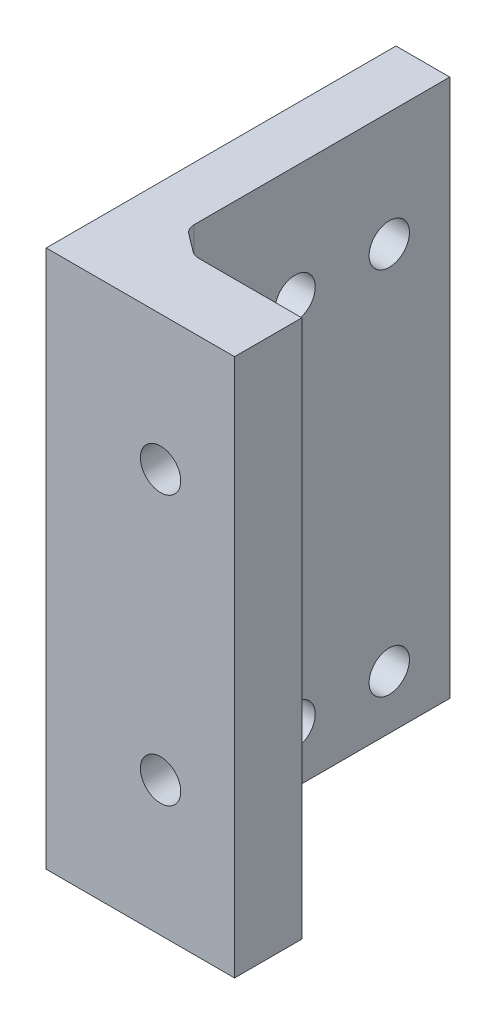
SolidWorks part; units mm, degrees
ref_plane "Front Plane" through (0, 0, 0) normal (0, 0, 1) x (1, 0, 0)
ref_plane "Top Plane" through (0, 0, 0) normal (0, 1, 0) x (1, 0, 0)
ref_plane "Right Plane" through (0, 0, 0) normal (1, 0, 0) x (0, 0, -1)
sketch "Sketch1" plane through (0, 0, 0) normal (0, 0, 1) x (1, 0, 0)
  line L6 (11, -20) -> (11, 19.3326) construction
  line L7 (15, -20) -> (11, -20)
  line L8 (15, -20) -> (15, 20)
  line L9 (15, 20) -> (11, 20)
  line L10 (11, -20) -> (11, 20)
  dimension "D1" = 11
  dimension "D2" = 4
extrude "Boss-Extrude2" add sketch "Sketch1" along normal blind 20 and the other way blind 4
sketch "Sketch3" plane through (15, 0, 0) normal (1, 0, 0) x (0, 0, -1)
  line L0 (4, 20) -> (-20, 20) construction
  line L6 (4, 20) -> (4, -20) construction
  line L7 (4, -20) -> (-20, -20) construction
  circle A2 centre (-7.5, -16) radius 1.5
  circle A6 centre (-7.5, 11.5) radius 1.5
  circle A8 centre (-0.5, 11.5) radius 1.5
  circle A9 centre (-0.5, -16) radius 1.5
  point P4 (0, 0)
  point P11 (0, 0)
  point P12 (0, 0)
  point P13 (0, 0)
  point P14 (0, 0)
  point P17 (0, 0)
  dimension "D1" = 3
  dimension "D3" = 3
  dimension "D4" = 4.5
  dimension "D5" = 4
  dimension "D6" = 3
  dimension "D7" = 7
  dimension "D8" = 4.5
  dimension "D9" = 8.5
  dimension "D2" = 3
extrude "Cut-Extrude1" cut sketch "Sketch3" against normal through all
sketch "Sketch4" plane through (15, 0, 0) normal (1, 0, 0) x (0, 0, -1)
  line L0 (-20, -20) -> (4, -20) construction
  line L1 (-20, 20) -> (-17, 20)
  line L2 (-20, 20) -> (-20, -20)
  line L3 (-20, -20) -> (-17, -20)
  line L4 (-17, 20) -> (-17, -20)
  dimension "D1" = 3
extrude "Boss-Extrude3" add sketch "Sketch4" along normal blind 10
sketch "Sketch5" plane through (0, 0, 17) normal (0, 0, -1) x (-1, 0, 0)
  line L0 (-15, -20) -> (-15, 20) construction
  line L1 (-25, -20) -> (-15, -20) construction
  line L2 (-25, 20) -> (-15, 20) construction
  circle A0 centre (-19.5, -10) radius 1.5
  circle A1 centre (-19.5, 10) radius 1.5
  dimension "D1" = 4.5
  dimension "D2" = 10
  dimension "D3" = 3
  dimension "D4" = 3
  dimension "D5" = 10
extrude "Cut-Extrude2" cut sketch "Sketch5" against normal through all
ref_plane "Plane1" through (15, 20, 17) normal (-1, 0, 0) x (0, 0, 1)
ref_plane "Plane2" through (15, 20, 17) normal (-1, 0, 0) x (0, 0, 1)
sketch "Sketch8" plane through (0, 0, 20) normal (0, 0, 1) x (1, 0, 0)
  line L1 (11, 20) -> (25, 20)
  line L2 (11, 20) -> (11, -20)
  line L3 (11, -20) -> (25, -20)
  line L4 (25, 20) -> (25, -20)
  circle A0 centre (19.5, 10) radius 1.5
  circle A1 centre (19.5, -10) radius 1.5
  dimension "D1" = 3
  dimension "D2" = 3
extrude "Boss-Extrude4" add sketch "Sketch8" along normal blind 2
sketch "Sketch9" plane through (0, -20, 0) normal (0, -1, 0) x (1, 0, 0)
  line L0 (17, 17) -> (15, 17)
  line L1 (25, 17) -> (15, 17) construction
  line L2 (15, 19.75) -> (15, 14.25) construction
  line L3 (15, 17) -> (15, 15.5)
  line L4 (15, 15.5) -> (17, 17)
  dimension "D1" = 2
  dimension "D2" = 1.5
extrude "Boss-Extrude5" add sketch "Sketch9" against normal up to surface (40 mm away) up to face at (17, 20, 11.6667)
fillet "Fillet3" radius 1 2 edges at (17, 0, 17) (15, 0, 15.5)
